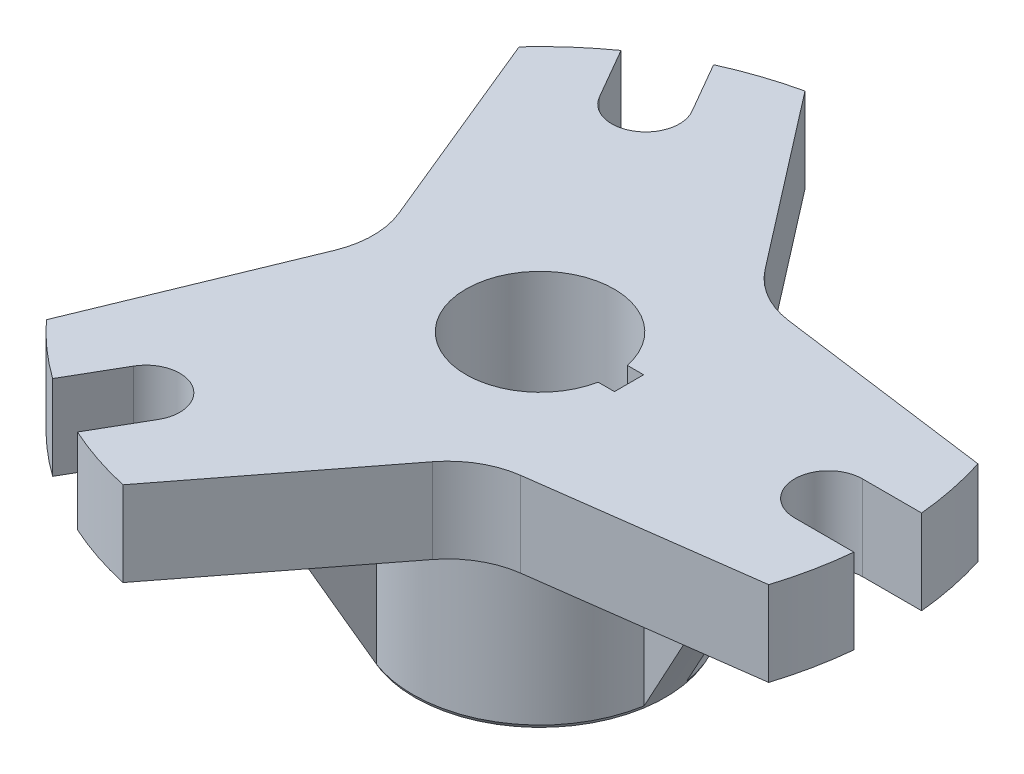
SolidWorks part; units mm, degrees
ref_plane "Front Plane" through (0, 0, 0) normal (0, 0, 1) x (1, 0, 0)
ref_plane "Top Plane" through (0, 0, 0) normal (0, 1, 0) x (1, 0, 0)
ref_plane "Right Plane" through (0, 0, 0) normal (1, 0, 0) x (0, 0, -1)
sketch "Sketch1" plane through (0, 0, 0) normal (0, 1, 0) x (1, 0, 0)
  circle A0 centre (0, 0) radius 82.5
  dimension "D1" = 165
extrude "Boss-Extrude1" add sketch "Sketch1" along normal blind 20
sketch "Sketch2" plane through (0, 0, 0) normal (0, -1, 0) x (1, 0, 0)
  circle A0 centre (0, 0) radius 30
  dimension "D1" = 60
extrude "Boss-Extrude2" add sketch "Sketch2" along normal blind 40
sketch "Sketch3" plane through (0, -40, 0) normal (0, -1, 0) x (1, 0, 0)
  circle A0 centre (0, 0) radius 17.5
  dimension "D1" = 35
extrude "Cut-Extrude1" cut sketch "Sketch3" against normal through all
sketch "Sketch4" plane through (0, 0, 0) normal (0, 0, 1) x (1, 0, 0)
  line L0 (26.0439, 0) -> (51.0439, 0)
  line L1 (-30, 0) -> (30, 0) construction
  line L2 (-82.5, 0) -> (82.5, 0) construction
  line L3 (51.0439, 0) -> (30, -40)
  line L4 (30, -40) -> (26.0439, -40)
  line L5 (-30, -40) -> (30, -40) construction
  line L6 (26.0439, -40) -> (26.0439, 0)
extrude "Boss-Extrude3" add sketch "Sketch4" along normal mid plane 10
pattern_circular "CirPattern4" count 3 over 360 about axis through (0, 0, 0) along (0, 1, 0) of "Boss-Extrude3"
sketch "Sketch5" plane through (0, 0, 0) normal (0, 0, 1) x (1, 0, 0)
  line L0 (51.0439, 0) -> (29.5804, -40)
  line L1 (29.5804, -40) -> (54.672, -40)
  line L2 (54.672, -40) -> (51.0439, 0)
  line L3 (0, 0) -> (0, -40) construction
  line L4 (-10.4601, -40) -> (29.5804, -40) construction
revolve "Cut-Revolve1" cut sketch "Sketch5" angle 360 about L3
sketch "Sketch7" plane through (0, 0, 0) normal (0, 0, 1) x (1, 0, 0)
  line L0 (-82.5, 0) -> (82.5, 0) construction
  line L1 (-82.5, 0) -> (82.5, 0) construction
  line L2 (0, 0) -> (82.5, 0)
sketch "Sketch8" plane through (0, 0, 0) normal (0, 1, 0) x (1, 0, 0)
  line L0 (0, 0) -> (-41.25, 71.4471)
  line L1 (0, 0) -> (-41.25, -71.4471)
  line L2 (0, 0) -> (82.5, 0) construction
  line L3 (-82.5, 0) -> (82.5, 0) construction
  circle A0 centre (0, 0) radius 82.5 construction
  dimension "D1" = 120
  dimension "D2" = 120
  dimension "D3" = 120
sketch "Sketch10" plane through (0, 0, 0) normal (0, 1, 0) x (1, 0, 0)
  line L0 (-60.7567, -55.811) -> (-40.9324, -7.607)
  line L1 (-82.5, 0) -> (82.5, 0) construction
  line L2 (-40.9324, 7.607) -> (-60.7567, 55.811)
  circle A0 centre (0, 0) radius 82.5 construction
  arc A1 (-40.9324, 7.607) -> (-40.9324, -7.607) centre (-59.4293, 0) cw
  arc A2 (-60.7567, -55.811) -> (-60.7567, 55.811) centre (0, 0) cw
  point P11 (-37.804, 0)
  dimension "D3" = 20
  dimension "D1" = 25
  dimension "D2" = 25
extrude "Cut-Extrude13" cut sketch "Sketch10" along normal through all contours A2 L0 A1 L2
pattern_circular "CirPattern5" count 3 over 360 about axis through (0, 0, 0) along (0, 1, 0) of "Cut-Extrude13"
sketch "Sketch11" plane through (0, 0, 0) normal (0, 1, 0) x (1, 0, 0)
  line L2 (68.1253, 8) -> (82.1112, 8)
  line L4 (68.1253, -8) -> (82.1112, -8)
  arc A0 (82.1112, -8) -> (82.1112, 8) centre (0, 0) ccw
  arc A1 (68.1253, 8) -> (68.1253, -8) centre (68.1253, 0) ccw
  point P6 (82.5, 0)
extrude "Cut-Extrude14" cut sketch "Sketch11" along normal through all
pattern_circular "CirPattern6" count 3 over 360 about axis through (0, 0, 0) along (0, 1, 0) of "Cut-Extrude14"
sketch "Sketch13" plane through (0, 0, 0) normal (0, 1, 0) x (1, 0, 0)
  line L0 (17.1573, 3.4462) -> (21.0159, 3.4462)
  line L4 (21.0159, 3.4462) -> (21.0159, -3.4462)
  line L7 (17.2694, -2.8319) -> (21.0159, -3.4462) construction
  line L8 (17.2694, 2.8319) -> (21.0159, 3.4462) construction
  line L9 (17.1573, -3.4462) -> (21.0159, -3.4462)
  arc A0 (17.1573, -3.4462) -> (17.1573, 3.4462) centre (0, 0) ccw
  arc A2 (-17.002, 4.145) -> (-17.2694, 2.8319) centre (0, 0) ccw
  point P0 (0, 0)
extrude "Cut-Extrude15" cut sketch "Sketch13" against normal through all both and the other way through all contours L4 L9 A0 L0
